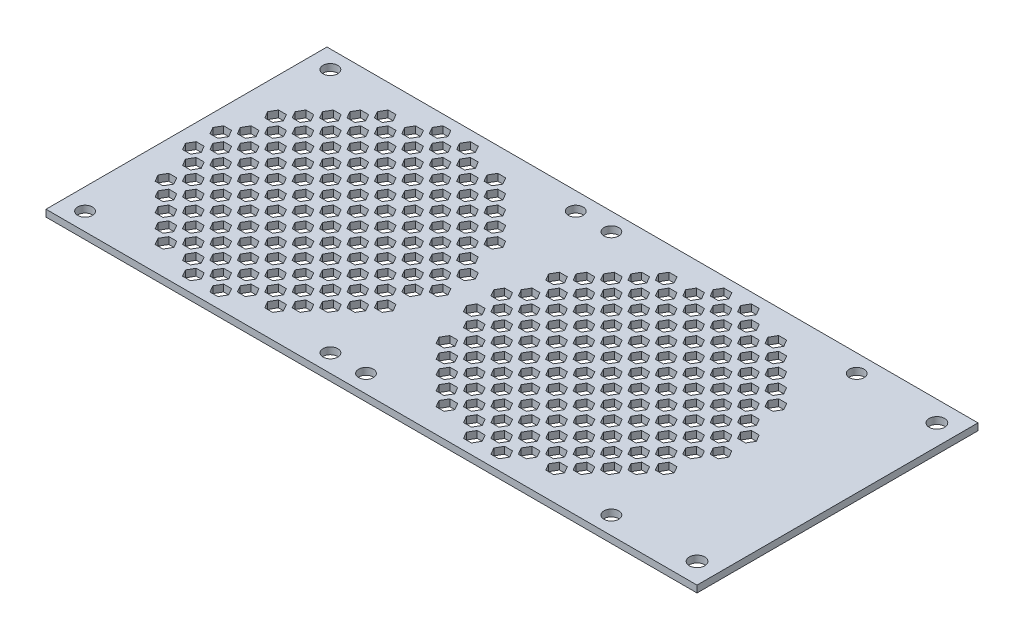
SolidWorks part; units mm, degrees
ref_plane "Front Plane" through (0, 0, 0) normal (0, 0, 1) x (1, 0, 0)
ref_plane "Top Plane" through (0, 0, 0) normal (0, 1, 0) x (1, 0, 0)
ref_plane "Right Plane" through (0, 0, 0) normal (1, 0, 0) x (0, 0, -1)
sketch "Sketch1" plane through (0, 0, 0) normal (0, 1, 0) x (1, 0, 0)
  line L1 (0, 0) -> (190, 0)
  line L2 (0, 0) -> (0, 82)
  line L3 (0, 82) -> (190, 82)
  line L4 (190, 0) -> (190, 82)
  dimension "D1" = 82
  dimension "D2" = 190
extrude "Boss-Extrude1" add sketch "Sketch1" along normal blind 2
hole_wizard "M4 Clearance Hole1" positions "Sketch2" profile "Sketch3" hole size "M4" standard "DIN" end condition up to next
sketch "Sketch2" plane through (0, 2, 0) normal (0, 1, 0) x (1, 0, 0)
  line L2 (0, 0) -> (190, 0) construction
  line L3 (190, 0) -> (190, 82) construction
  line L4 (190, 82) -> (0, 82) construction
  point P2 (184, 76)
  point P6 (184, 6)
  point P22 (0, 0)
  point P23 (0, 0)
  dimension "D1" = 6
  dimension "D3" = 6
  dimension "D4" = 6
sketch "Sketch3" plane through (184, 2, -76) normal (1, 0, 0) x (0, 0, 1)
  line L0 (0, 0) -> (0, 2)
  line L1 (0, 2) -> (2.25, 2)
  line L2 (2.25, 2) -> (2.25, 0)
  line L5 (2.25, 0) -> (0, 0)
  line L11 (0, -6.35) -> (0, 107.95) construction
  dimension "Thru Hole Dia." = 4.5
  dimension "Thru Hole Depth" = 2
sketch "Sketch4" plane through (0, 2, 0) normal (0, 1, 0) x (1, 0, 0)
  line L0 (0, 82) -> (0, 0) construction
  line L2 (51.1547, 43) -> (48.8453, 43)
  line L3 (43.1547, 43) -> (40.8453, 43)
  line L4 (40.8453, 43) -> (39.6906, 41)
  line L5 (39.6906, 41) -> (40.8453, 39)
  line L6 (40.8453, 39) -> (43.1547, 39)
  line L7 (43.1547, 39) -> (44.3094, 41)
  line L8 (44.3094, 41) -> (43.1547, 43)
  line L9 (48.8453, 43) -> (47.6906, 41)
  line L10 (47.6906, 41) -> (48.8453, 39)
  line L11 (48.8453, 39) -> (51.1547, 39)
  line L12 (51.1547, 39) -> (52.3094, 41)
  line L13 (52.3094, 41) -> (51.1547, 43)
  line L14 (59.1547, 43) -> (56.8453, 43)
  line L15 (56.8453, 43) -> (55.6906, 41)
  line L16 (55.6906, 41) -> (56.8453, 39)
  line L17 (56.8453, 39) -> (59.1547, 39)
  line L18 (59.1547, 39) -> (60.3094, 41)
  line L19 (60.3094, 41) -> (59.1547, 43)
  line L20 (67.1547, 43) -> (64.8453, 43)
  line L21 (64.8453, 43) -> (63.6906, 41)
  line L22 (63.6906, 41) -> (64.8453, 39)
  line L23 (64.8453, 39) -> (67.1547, 39)
  line L24 (67.1547, 39) -> (68.3094, 41)
  line L25 (68.3094, 41) -> (67.1547, 43)
  line L26 (75.1547, 43) -> (72.8453, 43)
  line L27 (72.8453, 43) -> (71.6906, 41)
  line L28 (71.6906, 41) -> (72.8453, 39)
  line L29 (72.8453, 39) -> (75.1547, 39)
  line L30 (75.1547, 39) -> (76.3094, 41)
  line L31 (76.3094, 41) -> (75.1547, 43)
  line L32 (51.1547, 51) -> (48.8453, 51)
  line L33 (48.8453, 51) -> (47.6906, 49)
  line L34 (47.6906, 49) -> (48.8453, 47)
  line L35 (48.8453, 47) -> (51.1547, 47)
  line L36 (51.1547, 47) -> (52.3094, 49)
  line L37 (52.3094, 49) -> (51.1547, 51)
  line L38 (59.1547, 51) -> (56.8453, 51)
  line L39 (56.8453, 51) -> (55.6906, 49)
  line L40 (55.6906, 49) -> (56.8453, 47)
  line L41 (56.8453, 47) -> (59.1547, 47)
  line L42 (59.1547, 47) -> (60.3094, 49)
  line L43 (60.3094, 49) -> (59.1547, 51)
  line L44 (67.1547, 51) -> (64.8453, 51)
  line L45 (64.8453, 51) -> (63.6906, 49)
  line L46 (63.6906, 49) -> (64.8453, 47)
  line L47 (64.8453, 47) -> (67.1547, 47)
  line L48 (67.1547, 47) -> (68.3094, 49)
  line L49 (68.3094, 49) -> (67.1547, 51)
  line L50 (75.1547, 51) -> (72.8453, 51)
  line L51 (72.8453, 51) -> (71.6906, 49)
  line L52 (71.6906, 49) -> (72.8453, 47)
  line L53 (72.8453, 47) -> (75.1547, 47)
  line L54 (75.1547, 47) -> (76.3094, 49)
  line L55 (76.3094, 49) -> (75.1547, 51)
  line L56 (51.1547, 59) -> (48.8453, 59)
  line L57 (48.8453, 59) -> (47.6906, 57)
  line L58 (47.6906, 57) -> (48.8453, 55)
  line L59 (48.8453, 55) -> (51.1547, 55)
  line L60 (51.1547, 55) -> (52.3094, 57)
  line L61 (52.3094, 57) -> (51.1547, 59)
  line L62 (59.1547, 59) -> (56.8453, 59)
  line L63 (56.8453, 59) -> (55.6906, 57)
  line L64 (55.6906, 57) -> (56.8453, 55)
  line L65 (56.8453, 55) -> (59.1547, 55)
  line L66 (59.1547, 55) -> (60.3094, 57)
  line L67 (60.3094, 57) -> (59.1547, 59)
  line L68 (67.1547, 59) -> (64.8453, 59)
  line L69 (64.8453, 59) -> (63.6906, 57)
  line L70 (63.6906, 57) -> (64.8453, 55)
  line L71 (64.8453, 55) -> (67.1547, 55)
  line L72 (67.1547, 55) -> (68.3094, 57)
  line L73 (68.3094, 57) -> (67.1547, 59)
  line L74 (75.1547, 59) -> (72.8453, 59)
  line L75 (72.8453, 59) -> (71.6906, 57)
  line L76 (71.6906, 57) -> (72.8453, 55)
  line L77 (72.8453, 55) -> (75.1547, 55)
  line L78 (75.1547, 55) -> (76.3094, 57)
  line L79 (76.3094, 57) -> (75.1547, 59)
  line L80 (51.1547, 67) -> (48.8453, 67)
  line L81 (48.8453, 67) -> (47.6906, 65)
  line L82 (47.6906, 65) -> (48.8453, 63)
  line L83 (48.8453, 63) -> (51.1547, 63)
  line L84 (51.1547, 63) -> (52.3094, 65)
  line L85 (52.3094, 65) -> (51.1547, 67)
  line L86 (59.1547, 67) -> (56.8453, 67)
  line L87 (56.8453, 67) -> (55.6906, 65)
  line L88 (55.6906, 65) -> (56.8453, 63)
  line L89 (56.8453, 63) -> (59.1547, 63)
  line L90 (59.1547, 63) -> (60.3094, 65)
  line L91 (60.3094, 65) -> (59.1547, 67)
  line L92 (67.1547, 67) -> (64.8453, 67)
  line L93 (64.8453, 67) -> (63.6906, 65)
  line L94 (63.6906, 65) -> (64.8453, 63)
  line L95 (64.8453, 63) -> (67.1547, 63)
  line L96 (67.1547, 63) -> (68.3094, 65)
  line L97 (68.3094, 65) -> (67.1547, 67)
  line L104 (51.1547, 75) -> (48.8453, 75)
  line L105 (48.8453, 75) -> (47.6906, 73)
  line L106 (47.6906, 73) -> (48.8453, 71)
  line L107 (48.8453, 71) -> (51.1547, 71)
  line L108 (51.1547, 71) -> (52.3094, 73)
  line L109 (52.3094, 73) -> (51.1547, 75)
  line L110 (59.1547, 75) -> (56.8453, 75)
  line L111 (56.8453, 75) -> (55.6906, 73)
  line L112 (55.6906, 73) -> (56.8453, 71)
  line L113 (56.8453, 71) -> (59.1547, 71)
  line L114 (59.1547, 71) -> (60.3094, 73)
  line L115 (60.3094, 73) -> (59.1547, 75)
  line L128 (43.1547, 51) -> (40.8453, 51)
  line L129 (40.8453, 51) -> (39.6906, 49)
  line L130 (39.6906, 49) -> (40.8453, 47)
  line L131 (40.8453, 47) -> (43.1547, 47)
  line L132 (43.1547, 47) -> (44.3094, 49)
  line L133 (44.3094, 49) -> (43.1547, 51)
  line L134 (43.1547, 59) -> (40.8453, 59)
  line L135 (40.8453, 59) -> (39.6906, 57)
  line L136 (39.6906, 57) -> (40.8453, 55)
  line L137 (40.8453, 55) -> (43.1547, 55)
  line L138 (43.1547, 55) -> (44.3094, 57)
  line L139 (44.3094, 57) -> (43.1547, 59)
  line L140 (43.1547, 67) -> (40.8453, 67)
  line L141 (40.8453, 67) -> (39.6906, 65)
  line L142 (39.6906, 65) -> (40.8453, 63)
  line L143 (40.8453, 63) -> (43.1547, 63)
  line L144 (43.1547, 63) -> (44.3094, 65)
  line L145 (44.3094, 65) -> (43.1547, 67)
  line L146 (43.1547, 75) -> (40.8453, 75)
  line L147 (40.8453, 75) -> (39.6906, 73)
  line L148 (39.6906, 73) -> (40.8453, 71)
  line L149 (40.8453, 71) -> (43.1547, 71)
  line L150 (43.1547, 71) -> (44.3094, 73)
  line L151 (44.3094, 73) -> (43.1547, 75)
  line L152 (75.1547, 75) -> (72.8453, 75) [skipped]
  line L153 (72.8453, 75) -> (71.6906, 73) [skipped]
  line L154 (71.6906, 73) -> (72.8453, 71) [skipped]
  line L155 (72.8453, 71) -> (75.1547, 71) [skipped]
  line L156 (75.1547, 71) -> (76.3094, 73) [skipped]
  line L157 (76.3094, 73) -> (75.1547, 75) [skipped]
  line L158 (67.1547, 75) -> (64.8453, 75) [skipped]
  line L159 (64.8453, 75) -> (63.6906, 73) [skipped]
  line L160 (63.6906, 73) -> (64.8453, 71) [skipped]
  line L161 (64.8453, 71) -> (67.1547, 71) [skipped]
  line L162 (67.1547, 71) -> (68.3094, 73) [skipped]
  line L163 (68.3094, 73) -> (67.1547, 75) [skipped]
  line L164 (75.1547, 67) -> (72.8453, 67) [skipped]
  line L165 (72.8453, 67) -> (71.6906, 65) [skipped]
  line L166 (71.6906, 65) -> (72.8453, 63) [skipped]
  line L167 (72.8453, 63) -> (75.1547, 63) [skipped]
  line L168 (75.1547, 63) -> (76.3094, 65) [skipped]
  line L169 (76.3094, 65) -> (75.1547, 67) [skipped]
  circle A0 centre (42, 41) radius 37.5 construction
  circle A2 centre (42, 41) radius 2 construction
  point P3 (0, 41)
  dimension "D1" = 75
  dimension "D2" = 4
  dimension "D3" = 42
  dimension "D4" = 5
  dimension "D6" = 8
  dimension "D7" = 8
  dimension "D5" = 5
extrude "Cut-Extrude1" cut sketch "Sketch4" against normal up to next (2 mm away)
sketch "Sketch5" plane through (0, 2, 0) normal (0, 1, 0) x (1, 0, 0)
  line L0 (56.3094, 45) -> (55.1547, 47)
  line L1 (48.3094, 45) -> (47.1547, 47)
  line L2 (47.1547, 47) -> (44.8453, 47)
  line L3 (44.8453, 47) -> (43.6906, 45)
  line L4 (43.6906, 45) -> (44.8453, 43)
  line L5 (44.8453, 43) -> (47.1547, 43)
  line L6 (47.1547, 43) -> (48.3094, 45)
  line L7 (55.1547, 47) -> (52.8453, 47)
  line L8 (52.8453, 47) -> (51.6906, 45)
  line L9 (51.6906, 45) -> (52.8453, 43)
  line L10 (52.8453, 43) -> (55.1547, 43)
  line L11 (55.1547, 43) -> (56.3094, 45)
  line L12 (64.3094, 45) -> (63.1547, 47)
  line L13 (63.1547, 47) -> (60.8453, 47)
  line L14 (60.8453, 47) -> (59.6906, 45)
  line L15 (59.6906, 45) -> (60.8453, 43)
  line L16 (60.8453, 43) -> (63.1547, 43)
  line L17 (63.1547, 43) -> (64.3094, 45)
  line L18 (72.3094, 45) -> (71.1547, 47)
  line L19 (71.1547, 47) -> (68.8453, 47)
  line L20 (68.8453, 47) -> (67.6906, 45)
  line L21 (67.6906, 45) -> (68.8453, 43)
  line L22 (68.8453, 43) -> (71.1547, 43)
  line L23 (71.1547, 43) -> (72.3094, 45)
  line L24 (80.3094, 45) -> (79.1547, 47)
  line L25 (79.1547, 47) -> (76.8453, 47)
  line L26 (76.8453, 47) -> (75.6906, 45)
  line L27 (75.6906, 45) -> (76.8453, 43)
  line L28 (76.8453, 43) -> (79.1547, 43)
  line L29 (79.1547, 43) -> (80.3094, 45)
  line L30 (56.3094, 53) -> (55.1547, 55)
  line L31 (55.1547, 55) -> (52.8453, 55)
  line L32 (52.8453, 55) -> (51.6906, 53)
  line L33 (51.6906, 53) -> (52.8453, 51)
  line L34 (52.8453, 51) -> (55.1547, 51)
  line L35 (55.1547, 51) -> (56.3094, 53)
  line L36 (64.3094, 53) -> (63.1547, 55)
  line L37 (63.1547, 55) -> (60.8453, 55)
  line L38 (60.8453, 55) -> (59.6906, 53)
  line L39 (59.6906, 53) -> (60.8453, 51)
  line L40 (60.8453, 51) -> (63.1547, 51)
  line L41 (63.1547, 51) -> (64.3094, 53)
  line L42 (72.3094, 53) -> (71.1547, 55)
  line L43 (71.1547, 55) -> (68.8453, 55)
  line L44 (68.8453, 55) -> (67.6906, 53)
  line L45 (67.6906, 53) -> (68.8453, 51)
  line L46 (68.8453, 51) -> (71.1547, 51)
  line L47 (71.1547, 51) -> (72.3094, 53)
  line L54 (56.3094, 61) -> (55.1547, 63)
  line L55 (55.1547, 63) -> (52.8453, 63)
  line L56 (52.8453, 63) -> (51.6906, 61)
  line L57 (51.6906, 61) -> (52.8453, 59)
  line L58 (52.8453, 59) -> (55.1547, 59)
  line L59 (55.1547, 59) -> (56.3094, 61)
  line L60 (64.3094, 61) -> (63.1547, 63)
  line L61 (63.1547, 63) -> (60.8453, 63)
  line L62 (60.8453, 63) -> (59.6906, 61)
  line L63 (59.6906, 61) -> (60.8453, 59)
  line L64 (60.8453, 59) -> (63.1547, 59)
  line L65 (63.1547, 59) -> (64.3094, 61)
  line L66 (72.3094, 61) -> (71.1547, 63)
  line L67 (71.1547, 63) -> (68.8453, 63)
  line L68 (68.8453, 63) -> (67.6906, 61)
  line L69 (67.6906, 61) -> (68.8453, 59)
  line L70 (68.8453, 59) -> (71.1547, 59)
  line L71 (71.1547, 59) -> (72.3094, 61)
  line L78 (56.3094, 69) -> (55.1547, 71)
  line L79 (55.1547, 71) -> (52.8453, 71)
  line L80 (52.8453, 71) -> (51.6906, 69)
  line L81 (51.6906, 69) -> (52.8453, 67)
  line L82 (52.8453, 67) -> (55.1547, 67)
  line L83 (55.1547, 67) -> (56.3094, 69)
  line L84 (64.3094, 69) -> (63.1547, 71)
  line L85 (63.1547, 71) -> (60.8453, 71)
  line L86 (60.8453, 71) -> (59.6906, 69)
  line L87 (59.6906, 69) -> (60.8453, 67)
  line L88 (60.8453, 67) -> (63.1547, 67)
  line L89 (63.1547, 67) -> (64.3094, 69)
  line L126 (48.3094, 53) -> (47.1547, 55)
  line L127 (47.1547, 55) -> (44.8453, 55)
  line L128 (44.8453, 55) -> (43.6906, 53)
  line L129 (43.6906, 53) -> (44.8453, 51)
  line L130 (44.8453, 51) -> (47.1547, 51)
  line L131 (47.1547, 51) -> (48.3094, 53)
  line L132 (48.3094, 61) -> (47.1547, 63)
  line L133 (47.1547, 63) -> (44.8453, 63)
  line L134 (44.8453, 63) -> (43.6906, 61)
  line L135 (43.6906, 61) -> (44.8453, 59)
  line L136 (44.8453, 59) -> (47.1547, 59)
  line L137 (47.1547, 59) -> (48.3094, 61)
  line L138 (48.3094, 69) -> (47.1547, 71)
  line L139 (47.1547, 71) -> (44.8453, 71)
  line L140 (44.8453, 71) -> (43.6906, 69)
  line L141 (43.6906, 69) -> (44.8453, 67)
  line L142 (44.8453, 67) -> (47.1547, 67)
  line L143 (47.1547, 67) -> (48.3094, 69)
  line L144 (48.3094, 77) -> (47.1547, 79)
  line L145 (47.1547, 79) -> (44.8453, 79)
  line L146 (44.8453, 79) -> (43.6906, 77)
  line L147 (43.6906, 77) -> (44.8453, 75)
  line L148 (44.8453, 75) -> (47.1547, 75)
  line L149 (47.1547, 75) -> (48.3094, 77)
  line L150 (80.3094, 53) -> (79.1547, 55) [skipped]
  line L151 (79.1547, 55) -> (76.8453, 55) [skipped]
  line L152 (76.8453, 55) -> (75.6906, 53) [skipped]
  line L153 (75.6906, 53) -> (76.8453, 51) [skipped]
  line L154 (76.8453, 51) -> (79.1547, 51) [skipped]
  line L155 (79.1547, 51) -> (80.3094, 53) [skipped]
  line L156 (80.3094, 61) -> (79.1547, 63) [skipped]
  line L157 (79.1547, 63) -> (76.8453, 63) [skipped]
  line L158 (76.8453, 63) -> (75.6906, 61) [skipped]
  line L159 (75.6906, 61) -> (76.8453, 59) [skipped]
  line L160 (76.8453, 59) -> (79.1547, 59) [skipped]
  line L161 (79.1547, 59) -> (80.3094, 61) [skipped]
  line L162 (80.3094, 69) -> (79.1547, 71) [skipped]
  line L163 (79.1547, 71) -> (76.8453, 71) [skipped]
  line L164 (76.8453, 71) -> (75.6906, 69) [skipped]
  line L165 (75.6906, 69) -> (76.8453, 67) [skipped]
  line L166 (76.8453, 67) -> (79.1547, 67) [skipped]
  line L167 (79.1547, 67) -> (80.3094, 69) [skipped]
  line L168 (72.3094, 69) -> (71.1547, 71) [skipped]
  line L169 (71.1547, 71) -> (68.8453, 71) [skipped]
  line L170 (68.8453, 71) -> (67.6906, 69) [skipped]
  line L171 (67.6906, 69) -> (68.8453, 67) [skipped]
  line L172 (68.8453, 67) -> (71.1547, 67) [skipped]
  line L173 (71.1547, 67) -> (72.3094, 69) [skipped]
  line L174 (80.3094, 77) -> (79.1547, 79) [skipped]
  line L175 (79.1547, 79) -> (76.8453, 79) [skipped]
  line L176 (76.8453, 79) -> (75.6906, 77) [skipped]
  line L177 (75.6906, 77) -> (76.8453, 75) [skipped]
  line L178 (76.8453, 75) -> (79.1547, 75) [skipped]
  line L179 (79.1547, 75) -> (80.3094, 77) [skipped]
  line L180 (72.3094, 77) -> (71.1547, 79) [skipped]
  line L181 (71.1547, 79) -> (68.8453, 79) [skipped]
  line L182 (68.8453, 79) -> (67.6906, 77) [skipped]
  line L183 (67.6906, 77) -> (68.8453, 75) [skipped]
  line L184 (68.8453, 75) -> (71.1547, 75) [skipped]
  line L185 (71.1547, 75) -> (72.3094, 77) [skipped]
  line L186 (64.3094, 77) -> (63.1547, 79) [skipped]
  line L187 (63.1547, 79) -> (60.8453, 79) [skipped]
  line L188 (60.8453, 79) -> (59.6906, 77) [skipped]
  line L189 (59.6906, 77) -> (60.8453, 75) [skipped]
  line L190 (60.8453, 75) -> (63.1547, 75) [skipped]
  line L191 (63.1547, 75) -> (64.3094, 77) [skipped]
  line L192 (56.3094, 77) -> (55.1547, 79) [skipped]
  line L193 (55.1547, 79) -> (52.8453, 79) [skipped]
  line L194 (52.8453, 79) -> (51.6906, 77) [skipped]
  line L195 (51.6906, 77) -> (52.8453, 75) [skipped]
  line L196 (52.8453, 75) -> (55.1547, 75) [skipped]
  line L197 (55.1547, 75) -> (56.3094, 77) [skipped]
  circle A0 centre (46, 45) radius 2 construction
  circle A1 centre (42, 41) radius 2 construction
  dimension "D1" = 4
  dimension "D2" = 4
  dimension "D5" = 8
  dimension "D6" = 8
  dimension "D3" = 5
  dimension "D4" = 5
extrude "Cut-Extrude2" cut sketch "Sketch5" against normal up to next (2 mm away)
ref_plane "Plane1" through (42, 0, 0) normal (-1, 0, 0) x (0, 0, 1)
ref_plane "Plane2" through (0, 0, -41) normal (0, 0, -1) x (-1, 0, 0)
ref_plane "Plane3" through (95, 0, 0) normal (-1, 0, 0) x (0, 0, 1)
mirror "Mirror1" about plane through (0, 0, -41) normal (0, 0, -1) of "Cut-Extrude1", "Cut-Extrude2"
mirror "Mirror2" about plane through (42, 0, 0) normal (-1, 0, 0) of "Mirror1", "Cut-Extrude1", "Cut-Extrude2"
pattern_linear "LPattern1" count 2 spacing 82 along (1, 0, 0) of "Cut-Extrude1", "Cut-Extrude2", "Mirror1", "Mirror2"
hole_wizard "M4 Clearance Hole2" positions "Sketch8" profile "Sketch7" hole size "M4" standard "DIN"
sketch "Sketch8" plane through (0, 2, 0) normal (0, 1, 0) x (1, 0, 0)
  line L1 (6.2, 5.2) -> (77.8, 5.2) construction
  line L2 (6.2, 5.2) -> (6.2, 76.8) construction
  line L3 (6.2, 76.8) -> (77.8, 76.8) construction
  line L4 (77.8, 5.2) -> (77.8, 76.8) construction
  line L5 (6.2, 5.2) -> (77.8, 76.8) construction
  line L6 (6.2, 76.8) -> (77.8, 5.2) construction
  line L8 (88.2, 5.2) -> (159.8, 5.2) construction
  line L9 (88.2, 5.2) -> (88.2, 76.8) construction
  line L10 (88.2, 76.8) -> (159.8, 76.8) construction
  line L11 (159.8, 5.2) -> (159.8, 76.8) construction
  line L12 (88.2, 5.2) -> (159.8, 76.8) construction
  line L13 (88.2, 76.8) -> (159.8, 5.2) construction
  line L14 (43.1547, 43) -> (40.8453, 43) construction
  line L15 (125.1547, 43) -> (122.8453, 43) construction
  point P5 (77.8, 76.8)
  point P102 (6.2, 5.2)
  point P103 (6.2, 76.8)
  point P104 (77.8, 5.2)
  point P106 (159.8, 76.8)
  point P195 (88.2, 5.2)
  point P196 (88.2, 76.8)
  point P197 (159.8, 5.2)
  point P201 (42, 41)
  point P204 (42, 43)
  point P206 (124, 41)
  point P209 (124, 43)
  dimension "D1" = 71.6
sketch "Sketch7" plane through (77.8, 2, -76.8) normal (1, 0, 0) x (0, 0, 1)
  line L0 (0, 0) -> (0, 2)
  line L1 (0, 2) -> (2.15, 2)
  line L2 (2.15, 2) -> (2.15, 0)
  line L5 (2.15, 0) -> (0, 0)
  line L11 (0, -6.35) -> (0, 107.95) construction
  dimension "Thru Hole Dia." = 4.3
  dimension "Thru Hole Depth" = 2
